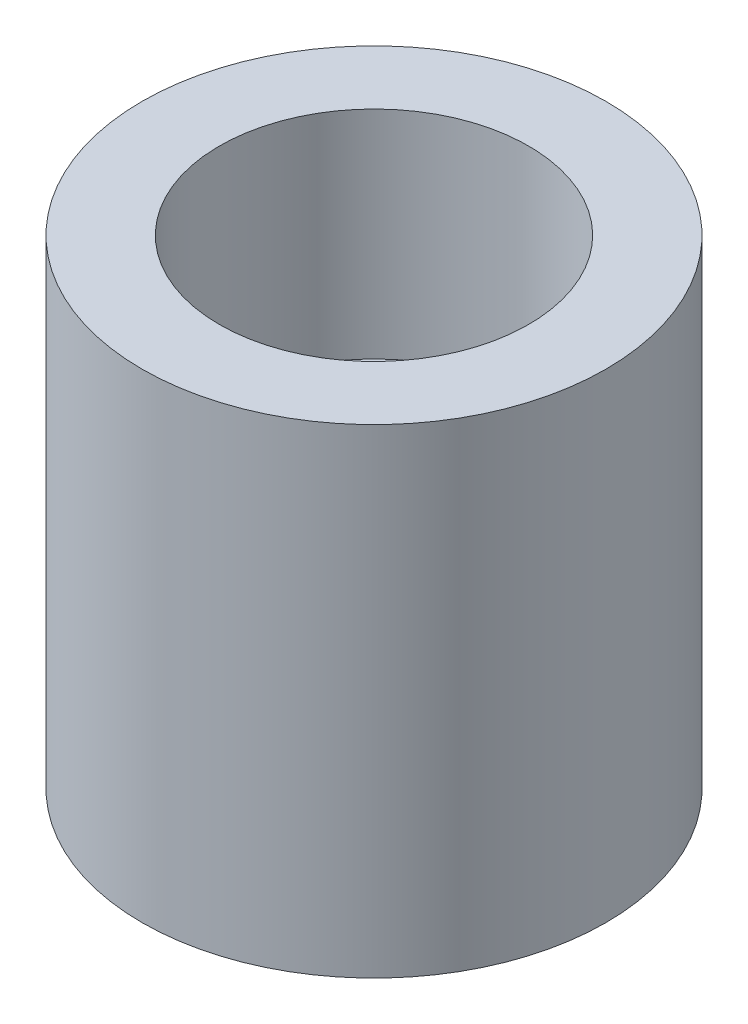
SolidWorks part; units mm, degrees
ref_plane "Front Plane" through (0, 0, 0) normal (0, 0, 1) x (1, 0, 0)
ref_plane "Top Plane" through (0, 0, 0) normal (0, 1, 0) x (1, 0, 0)
ref_plane "Right Plane" through (0, 0, 0) normal (1, 0, 0) x (0, 0, -1)
sketch "Sketch1" plane through (0, 0, 0) normal (0, 1, 0) x (1, 0, 0)
  circle A0 centre (0, 0) radius 7.5
  dimension "D1" = 15
extrude "Boss-Extrude1" add sketch "Sketch1" along normal blind 15.5
sketch "Sketch2" plane through (0, 15.5, 0) normal (0, 1, 0) x (1, 0, 0)
  circle A0 centre (0, 0) radius 5
  dimension "D1" = 10
extrude "Cut-Extrude1" cut sketch "Sketch2" against normal blind 7
